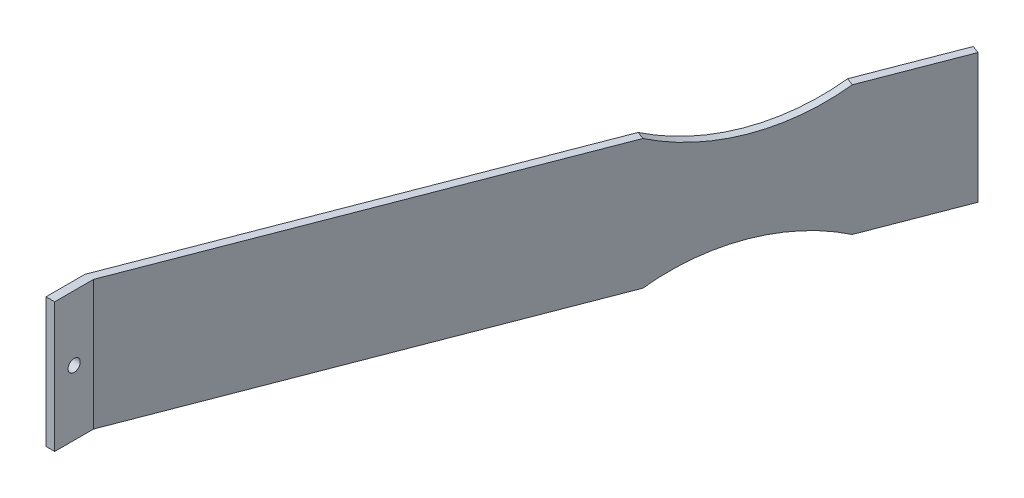
SolidWorks part; units mm, degrees
material "Acrylic (Medium-high impact)"
ref_plane "Front Plane" through (0, 0, 0) normal (0, 0, 1) x (1, 0, 0)
ref_plane "Top Plane" through (0, 0, 0) normal (0, 1, 0) x (1, 0, 0)
ref_plane "Right Plane" through (0, 0, 0) normal (1, 0, 0) x (0, 0, -1)
sketch "Sketch1" plane through (0, 0, 0) normal (0, 1, 0) x (1, 0, 0)
  line L0 (0, 132.715) -> (0, -132.715) construction
  line L1 (-279.4, -132.715) -> (279.4, -132.715) construction
  line L2 (-279.4, -132.715) -> (-279.4, 132.715) construction
  line L4 (279.4, -132.715) -> (279.4, 132.715) construction
  line L5 (-179.705, 132.715) -> (179.705, 132.715) construction
  line L6 (-279.4, 0) -> (279.4, 0) construction
  line L7 (-179.705, 132.715) -> (-279.4, 132.715) construction
  line L8 (179.705, 132.715) -> (279.4, 132.715) construction
  line L9 (-279.4, -117.475) -> (-182.6681, 133.8554)
  line L10 (-275.998, -117.475) -> (-179.705, 132.715)
  line L11 (-280.5736, -120.5242) -> (-182.6681, 133.8554) construction
  line L12 (-277.6105, -121.6646) -> (-179.705, 132.715) construction
  line L13 (-182.6681, 133.8554) -> (-179.705, 132.715)
  line L14 (-279.4, -117.475) -> (-279.4, -132.715)
  line L15 (-275.998, -117.475) -> (-275.998, -132.715)
  line L16 (-279.4, -132.715) -> (-275.998, -132.715)
  line L17 (-279.4, -117.475) -> (-275.998, -117.475) construction
  line L18 (-279.4, -125.095) -> (-275.998, -125.095) construction
  point P0 (0, 0)
  point P12 (0, 132.715)
  dimension "D1" = 558.8
  dimension "D2" = 265.43
  dimension "D3" = 359.41
  dimension "D5" = 7.62
  dimension "D4" = 3.175
extrude "Boss-Extrude1" add sketch "Sketch1" along normal blind 50.8
sketch "Sketch2" plane through (-279.4, 0, 0) normal (-1, 0, 0) x (0, 0, 1)
  line L0 (125.095, 50.8) -> (125.095, 0) construction
  line L1 (117.475, 50.8) -> (132.715, 50.8) construction
  line L2 (117.475, 0) -> (132.715, 0) construction
  line L4 (117.475, 50.8) -> (117.475, 0) construction
  line L5 (117.475, 25.4) -> (132.715, 25.4) construction
  line L6 (132.715, 50.8) -> (132.715, 0) construction
  circle A0 centre (125.095, 25.4) radius 2.3813
  dimension "D1" = 4.7625
extrude "Cut-Extrude1" cut sketch "Sketch2" against normal through all both
sketch "Sketch3" plane through (-201.0085, 0, -77.364) normal (0.9333, 0, 0.3592) x (0.3592, 0, -0.9333)
  line L0 (-42.2909, 50.8) -> (21.2091, 50.8)
  line L1 (-208.7718, 50.8) -> (59.3091, 50.8) construction
  line L2 (59.3091, 50.8) -> (59.3091, 0) construction
  line L3 (-208.7718, 25.4) -> (59.3091, 25.4) construction
  line L4 (-208.7718, 50.8) -> (-208.7718, 0) construction
  line L5 (-42.2909, 0) -> (21.2091, 0)
  arc A0 (-42.2909, 50.8) -> (21.2091, 50.8) centre (-10.5409, 113.1358) ccw
  arc A1 (-42.2909, 0) -> (21.2091, 0) centre (-10.5409, -62.3358) cw
  point P5 (-10.5409, 43.18)
  dimension "D1" = 63.5
  dimension "D2" = 38.1
  dimension "D3" = 7.62
extrude "Cut-Extrude2" cut sketch "Sketch3" against normal through all both
